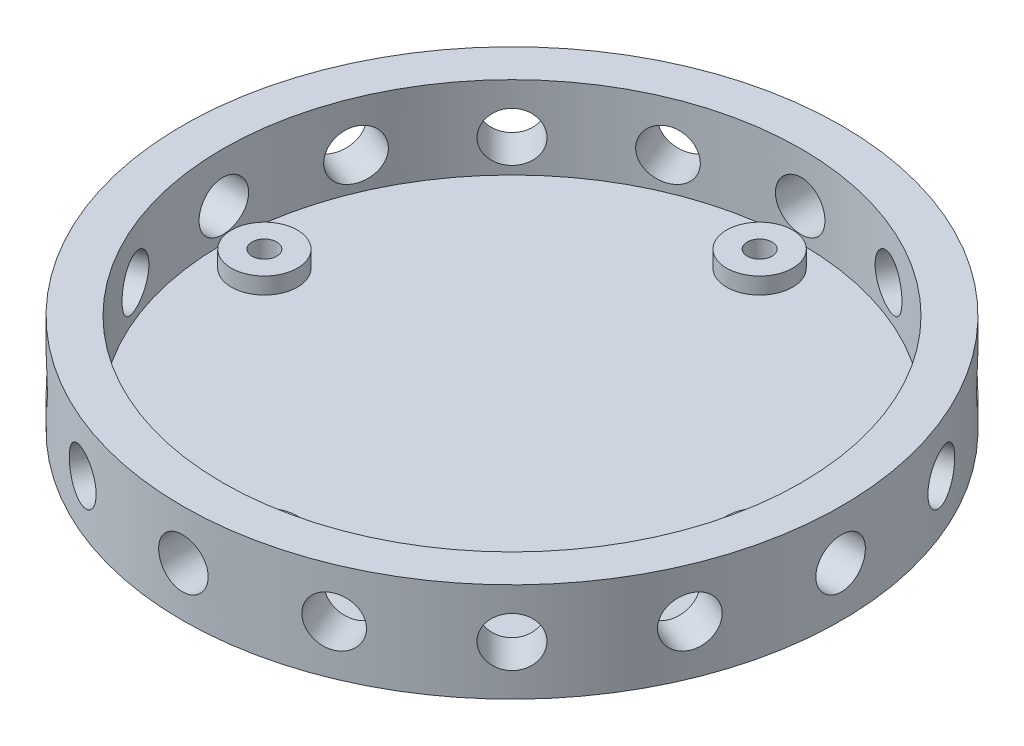
SolidWorks part; units mm, degrees
ref_plane "Front Plane" through (0, 0, 0) normal (0, 0, 1) x (1, 0, 0)
ref_plane "Top Plane" through (0, 0, 0) normal (0, 1, 0) x (1, 0, 0)
ref_plane "Right Plane" through (0, 0, 0) normal (1, 0, 0) x (0, 0, -1)
sketch "Sketch1" plane through (0, 0, 0) normal (0, 1, 0) x (1, 0, 0)
  circle A0 centre (0, 0) radius 63.373
  dimension "D1" = 126.746
extrude "Boss-Extrude1" add sketch "Sketch1" along normal blind 3.175
sketch "Sketch2" plane through (0, 3.175, 0) normal (0, 1, 0) x (1, 0, 0)
  circle A1 centre (0, 0) radius 63.373
  circle A3 centre (0, 0) radius 55.626
  dimension "D1" = 111.252
  dimension "D2" = 126.746
extrude "Boss-Extrude2" add sketch "Sketch2" along normal blind 15.875
sketch "Sketch9" plane through (0, 0, 0) normal (0, 0, 1) x (1, 0, 0)
  line L0 (0, 0) -> (0, 19.05) construction
  line L1 (55.626, 19.05) -> (-55.626, 19.05) construction
  circle A0 centre (0, 9.525) radius 4.7625
  dimension "D1" = 9.525
extrude "Cut-Extrude2" cut sketch "Sketch9" against normal through all
pattern_circular "CirPattern5" count 16 over 360 about axis through (0, 19.05, 0) along (0, -1, 0) of "Cut-Extrude2"
sketch "Sketch4" plane through (0, 3.175, 0) normal (0, 1, 0) x (1, 0, 0)
  line L0 (0, 0) -> (0, -55.626) construction
  line L1 (0, 0) -> (-55.626, 0) construction
  line L2 (-55.626, 0) -> (-53.975, 0) construction
  line L3 (-53.975, 0) -> (-47.625, 0) construction
  circle A0 centre (0, 0) radius 55.626 construction
  circle A1 centre (0, 0) radius 55.626 construction
  circle A2 centre (-47.625, 0) radius 6.35
  circle A3 centre (-47.625, 0) radius 2.3812
  dimension "D2" = 6.35
  dimension "D3" = 4.7625
  dimension "D1" = 1.651
extrude "Boss-Extrude4" add sketch "Sketch4" along normal blind 3.175
pattern_circular "CirPattern1" count 4 over 360 about axis through (0, 0, 0) along (0, 1, 0) of "Boss-Extrude4"
sketch "Sketch8" plane through (0, 19.05, 0) normal (0, 1, 0) x (1, 0, 0)
  circle A0 centre (-57.0304, -0.8343) radius 0.0294
  circle A4 centre (-47.625, 0) radius 2.3812
extrude "Cut-Extrude1" cut sketch "Sketch8" against normal through all
pattern_circular "CirPattern3" count 4 over 360 about axis through (0, 0, 0) along (0, 1, 0) of "Cut-Extrude1"
